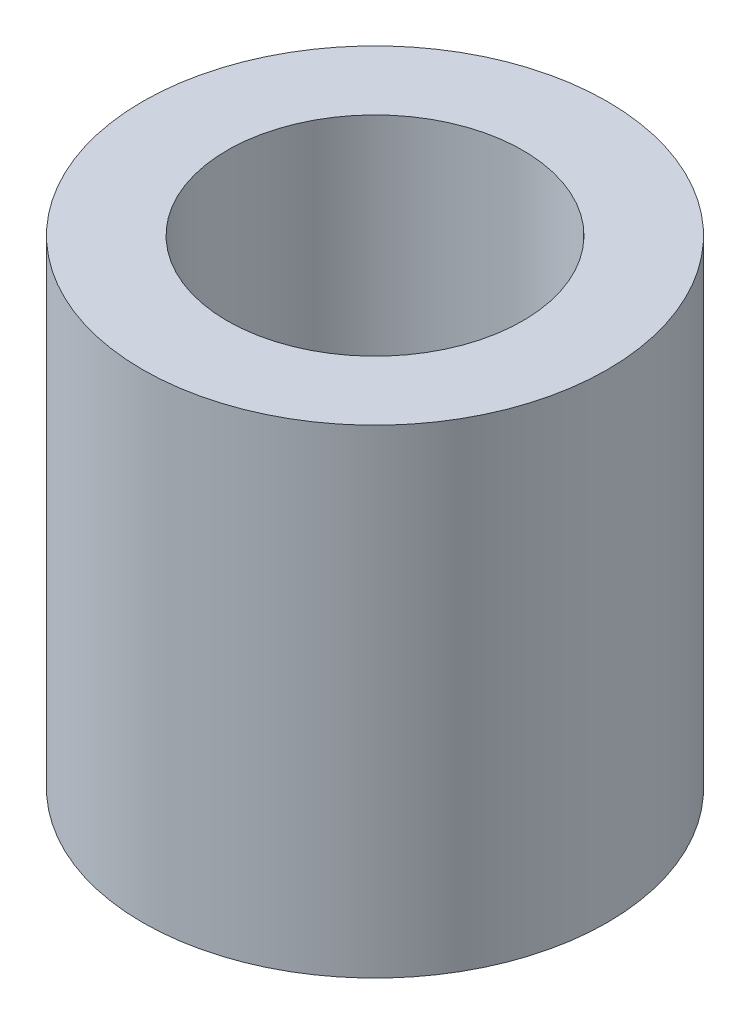
SolidWorks part; units mm, degrees
ref_plane "Front Plane" through (0, 0, 0) normal (0, 0, 1) x (1, 0, 0)
ref_plane "Top Plane" through (0, 0, 0) normal (0, 1, 0) x (1, 0, 0)
ref_plane "Right Plane" through (0, 0, 0) normal (1, 0, 0) x (0, 0, -1)
sketch "Sketch1" plane through (0, 0, 0) normal (0, 1, 0) x (1, 0, 0)
  circle A0 centre (0, 0) radius 3.175
  circle A1 centre (0, 0) radius 4.9911
  dimension "D1" = 6.35
  dimension "D2" = 9.9822
extrude "Boss-Extrude1" add sketch "Sketch1" along normal blind 10.287
